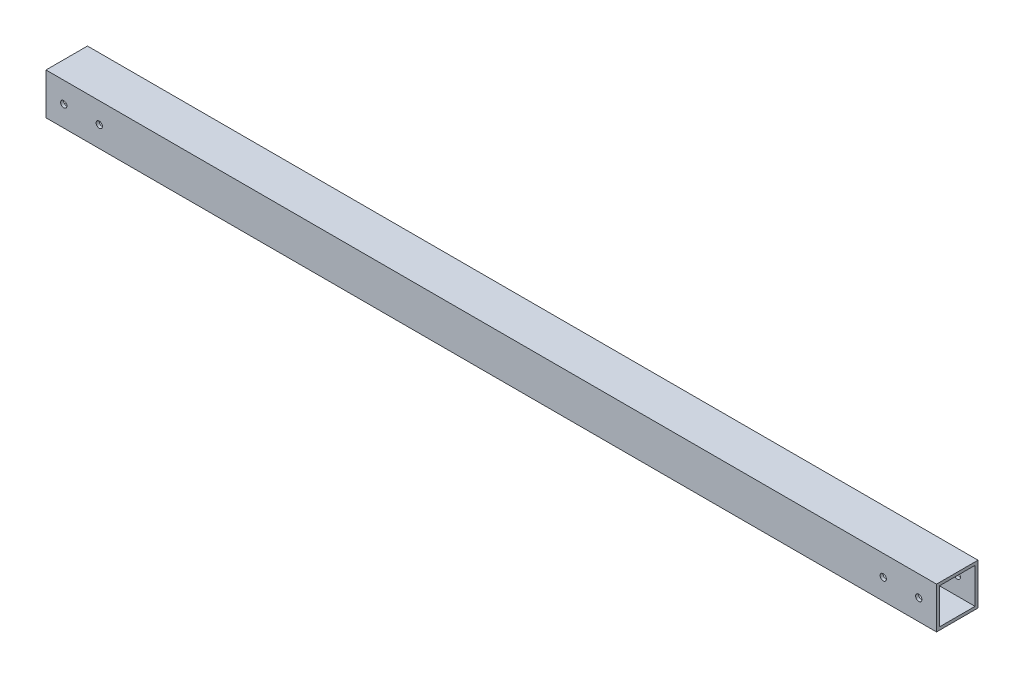
SolidWorks part; units mm, degrees
material "6061 Alloy"
ref_plane "Front Plane" through (0, 0, 0) normal (0, 0, 1) x (1, 0, 0)
ref_plane "Top Plane" through (0, 0, 0) normal (0, 1, 0) x (1, 0, 0)
ref_plane "Right Plane" through (0, 0, 0) normal (1, 0, 0) x (0, 0, -1)
sketch "Sketch1" plane through (0, 0, 0) normal (1, 0, 0) x (0, 0, -1)
  line L0 (3.175, 3.175) -> (3.175, 41.275)
  line L1 (0, 0) -> (44.45, 0)
  line L2 (0, 0) -> (0, 44.45)
  line L3 (0, 44.45) -> (44.45, 44.45)
  line L4 (44.45, 0) -> (44.45, 44.45)
  line L5 (3.175, 41.275) -> (41.275, 41.275)
  line L6 (41.275, 3.175) -> (41.275, 41.275)
  line L7 (3.175, 3.175) -> (41.275, 3.175)
  dimension "D1" = 44.45
  dimension "D2" = 3.175
extrude "Boss-Extrude1" add sketch "Sketch1" along normal blind 954.786
hole_wizard "1/4 Clearance Hole1" positions "Sketch2" profile "Sketch3" hole size "1/4" standard "ANSI Inch" end condition through all
sketch "Sketch2" plane through (0, 0, 0) normal (0, 0, 1) x (1, 0, 0)
  line L0 (0, 22.225) -> (954.786, 22.225) construction
  line L1 (0, 44.45) -> (0, 0) construction
  line L2 (954.786, 44.45) -> (954.786, 0) construction
  point P0 (19.05, 22.225)
  point P2 (57.15, 22.225)
  point P4 (935.736, 22.225)
  point P6 (897.636, 22.225)
  dimension "D1" = 19.05
  dimension "D2" = 38.1
  dimension "D3" = 19.05
  dimension "D4" = 38.1
sketch "Sketch3" plane through (19.05, 22.225, 0) normal (1, 0, 0) x (0, -1, 0)
  line L0 (0, 0) -> (0, 44.45)
  line L1 (0, 44.45) -> (3.3782, 44.45)
  line L2 (3.3782, 44.45) -> (3.3782, 0)
  line L5 (3.3782, 0) -> (0, 0)
  line L11 (0, -6.35) -> (0, 107.95) construction
  dimension "Thru Hole Dia." = 6.7564
  dimension "Thru Hole Depth" = 44.45
